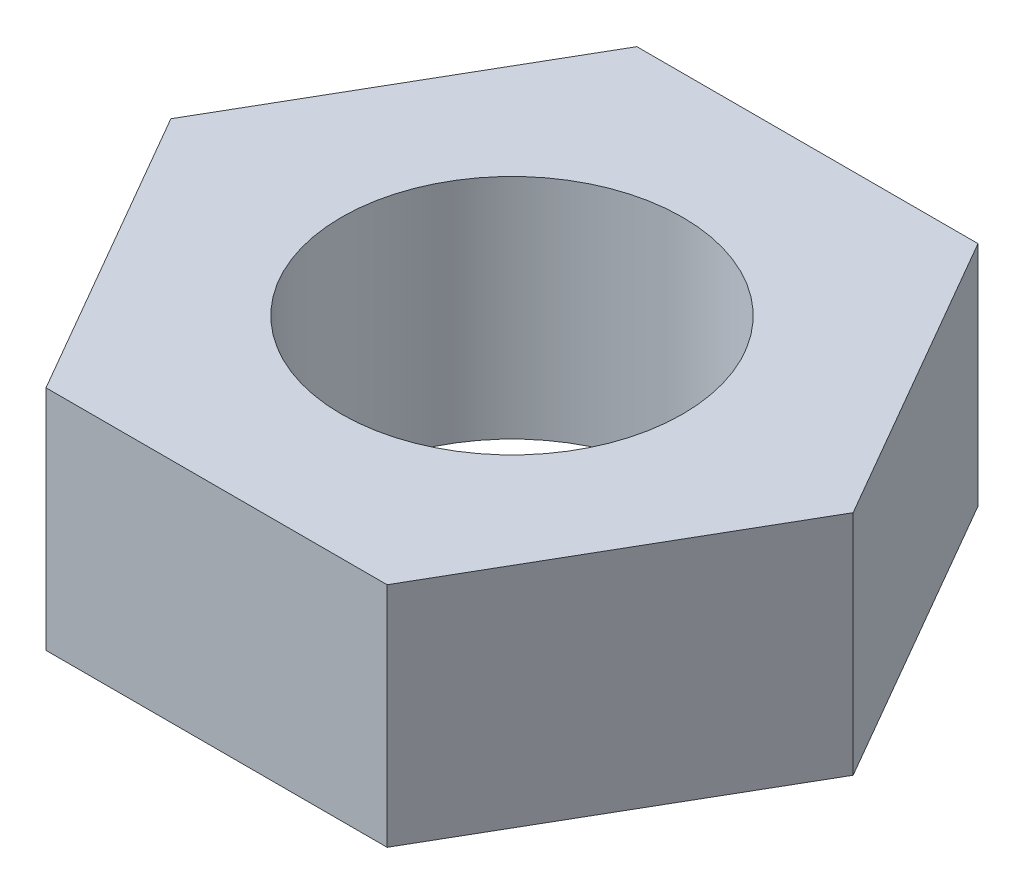
SolidWorks part; units mm, degrees
ref_plane "Front" through (0, 0, 0) normal (0, 0, 1) x (1, 0, 0)
ref_plane "Top" through (0, 0, 0) normal (0, 1, 0) x (1, 0, 0)
ref_plane "Right" through (0, 0, 0) normal (1, 0, 0) x (0, 0, -1)
sketch "草图1" plane through (0, 0, 0) normal (0, 1, 0) x (1, 0, 0)
  line L1 (-3.1172, 2.626) -> (-2.3672, 1.3269)
  line L2 (-2.3672, 1.3269) -> (-0.8672, 1.3269)
  line L3 (-0.8672, 1.3269) -> (-0.1172, 2.626)
  line L4 (-0.1172, 2.626) -> (-0.8672, 3.925)
  line L5 (-0.8672, 3.925) -> (-2.3672, 3.925)
  line L6 (-2.3672, 3.925) -> (-3.1172, 2.626)
  circle A0 centre (-1.6172, 2.626) radius 1.299 construction
  dimension "D1" = 1.5
extrude "凸台-拉伸1" add sketch "草图1" along normal blind 1
sketch "草图2" plane through (0, 1, 0) normal (0, 1, 0) x (1, 0, 0)
  circle A0 centre (-1.6172, 2.626) radius 0.75
  dimension "D1" = 1.5
extrude "切除-拉伸1" cut sketch "草图2" against normal blind 2
